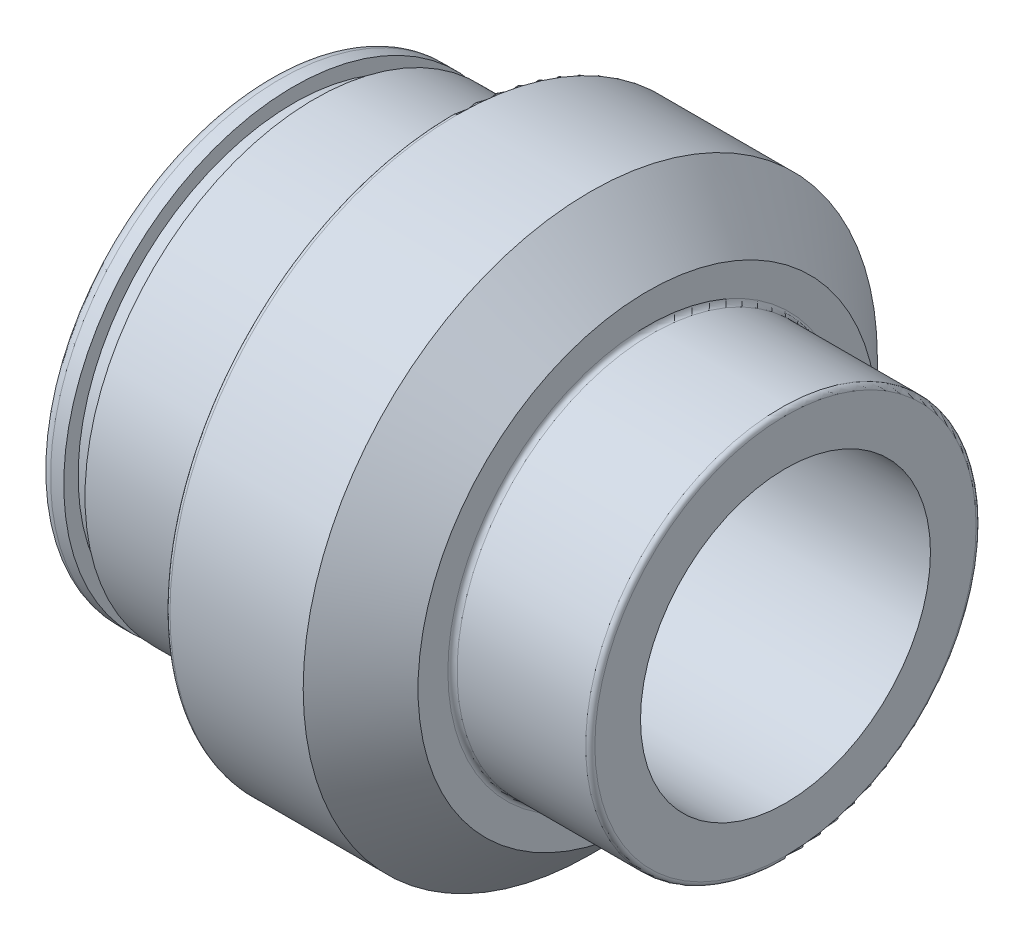
SolidWorks part; units mm, degrees
ref_plane "Plane1" through (0, 0, 0) normal (0, 0, 1) x (1, 0, 0)
ref_plane "Plane2" through (0, 0, 0) normal (0, 1, 0) x (1, 0, 0)
ref_plane "Plane3" through (0, 0, 0) normal (1, 0, 0) x (0, 0, -1)
sketch "Sketch1" plane through (0, 0, 0) normal (0, 0, 1) x (1, 0, 0)
  line L0 (0, 12.625) -> (0, 16.6)
  line L1 (-0.4, 17) -> (-11.6, 17)
  line L2 (-45, 19) -> (-45, 7)
  line L3 (-27, 12.625) -> (-30.2476, 7)
  line L5 (-12, 17.4) -> (-12, 20)
  line L6 (-17, 25) -> (-28.6, 25)
  line L7 (-29, 24.6) -> (-29, 20.4)
  line L8 (-29.4, 20) -> (-41, 20)
  line L9 (-41, 20) -> (-41, 18.75)
  line L10 (-41, 18.75) -> (-42.85, 18.75)
  line L11 (-42.85, 18.75) -> (-42.85, 20)
  line L12 (-27, 12.625) -> (0, 12.625)
  line L13 (0, 0) -> (-50, 0) construction
  line L14 (-42.85, 20) -> (-44, 20)
  line L15 (-30.2476, 7) -> (-45, 7)
  line L16 (-17, 25) -> (-12, 20)
  arc A0 (-44, 20) -> (-45, 19) centre (-44, 19) ccw
  arc A1 (-11.6, 17) -> (-12, 17.4) centre (-11.6, 17.4) cw
  arc A2 (-29, 24.6) -> (-28.6, 25) centre (-28.6, 24.6) cw
  arc A3 (-0.4, 17) -> (0, 16.6) centre (-0.4, 16.6) cw
  arc A4 (-29, 20.4) -> (-29.4, 20) centre (-29.4, 20.4) cw
  dimension "D5" = 4
  dimension "D11" = 0.4
  dimension "D17" = 1
  dimension "D19" = 0.4
  dimension "D22" = 0.4
  dimension "D3" = 34
  dimension "D4" = 25.25
  dimension "D6" = 27
  dimension "D7" = 60
  dimension "D8" = 45
  dimension "D9" = 12
  dimension "D10" = 50
  dimension "D12" = 14
  dimension "D13" = 1.85
  dimension "D14" = 37.5
  dimension "D15" = 12
  dimension "D16" = 40
  dimension "D20" = 45
  dimension "D21" = 5
revolve "Base-Revolve" add sketch "Sketch1" angle 360 about L13
cosmetic thread "Cosmetic Thread1" parameters "D2"=16
